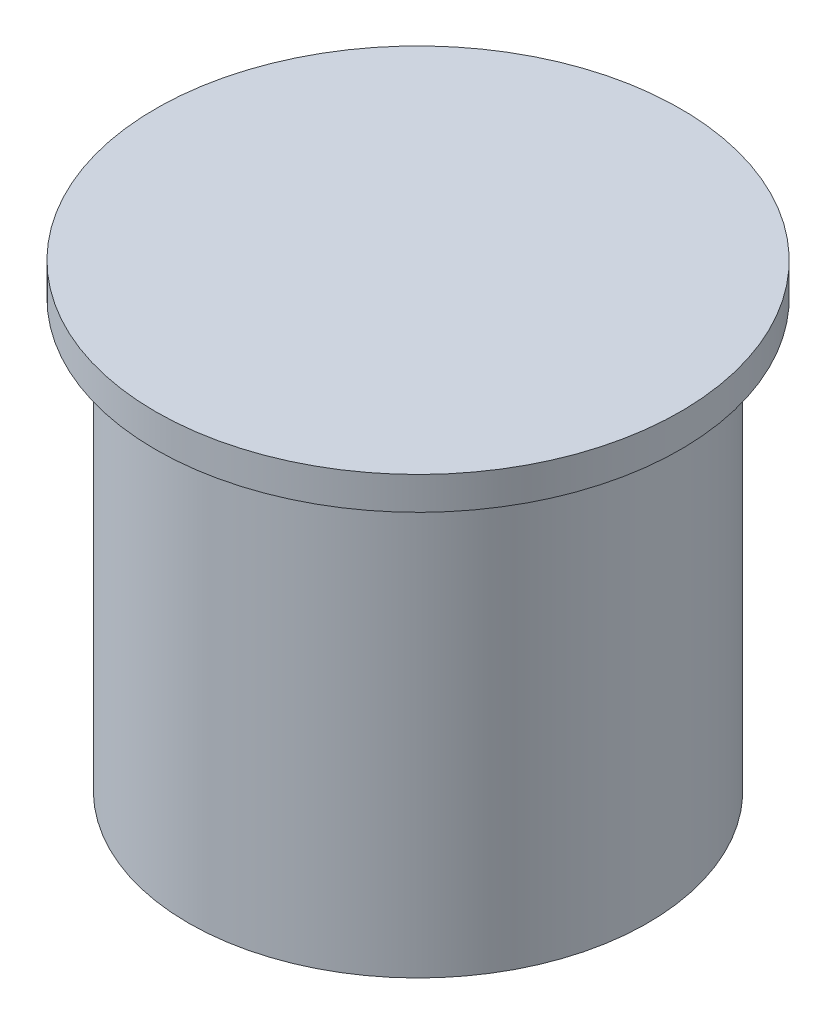
SolidWorks part; units mm, degrees
ref_plane "前基準面" through (0, 0, 0) normal (0, 0, 1) x (1, 0, 0)
ref_plane "上基準面" through (0, 0, 0) normal (0, 1, 0) x (1, 0, 0)
ref_plane "右基準面" through (0, 0, 0) normal (1, 0, 0) x (0, 0, -1)
sketch "草圖1" plane through (0, 0, 0) normal (0, 0, 1) x (1, 0, 0)
  line L0 (0, 18.0114) -> (0, -3.1783) construction
  line L1 (0, 14) -> (8, 14)
  line L2 (8, 14) -> (8, 13)
  line L3 (8, 13) -> (7, 13)
  line L4 (7, 13) -> (7, 0)
  line L5 (7, 0) -> (0, 0)
  line L6 (0, 0) -> (0, 14)
  point P7 (0, 12.2475)
  point P10 (0, -3.1783)
  point P11 (0, 18.0114)
  dimension "D1" = 14
  dimension "D2" = 13
  dimension "D3" = 1
  dimension "D4" = 16
revolve "旋轉1" add sketch "草圖1" angle 360 about L0
